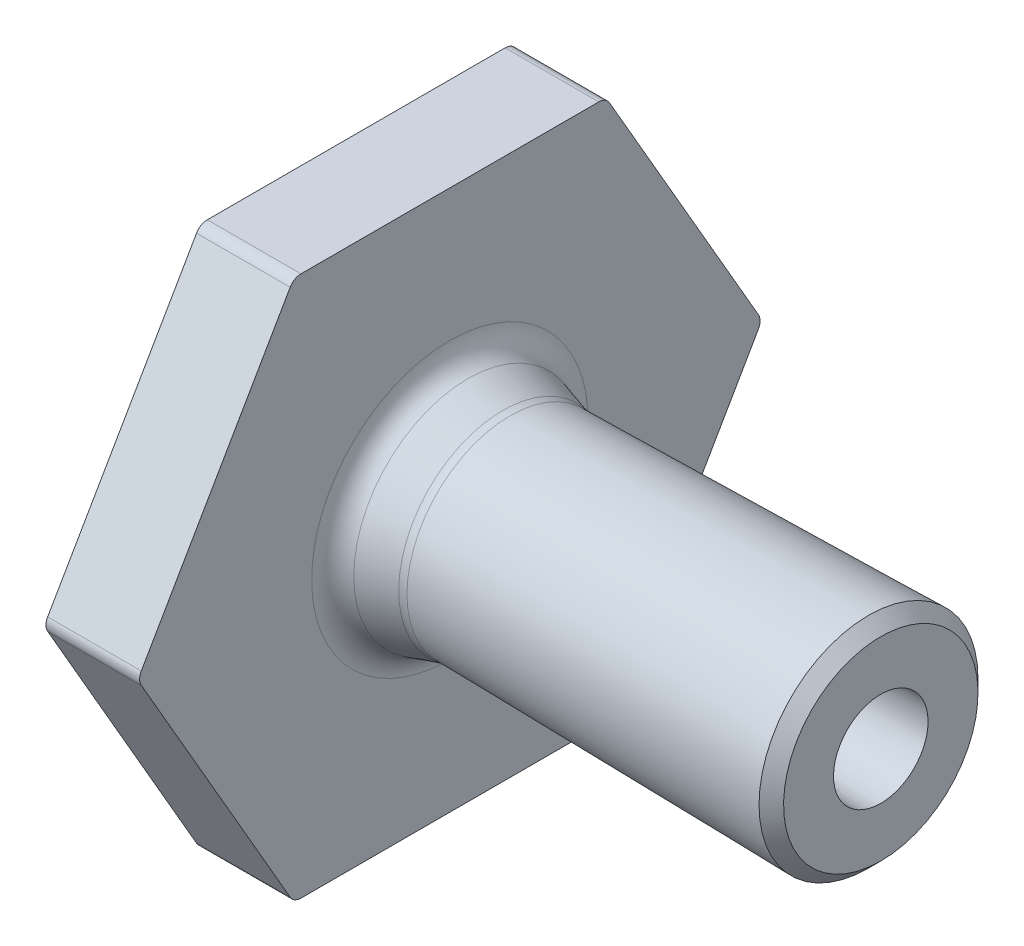
SolidWorks part; units mm, degrees
ref_plane "Front Plane" through (0, 0, 0) normal (0, 0, 1) x (1, 0, 0)
ref_plane "Top Plane" through (0, 0, 0) normal (0, 1, 0) x (1, 0, 0)
ref_plane "Right Plane" through (0, 0, 0) normal (1, 0, 0) x (0, 0, -1)
sketch "Sketch1" plane through (0, 0, 0) normal (0, 0, 1) x (1, 0, 0)
  line L0 (0, 1.825) -> (6.7189, 1.825)
  line L1 (0, -55) -> (0, 55) construction
  line L2 (6.7189, 1.825) -> (8.5498, 1.3)
  line L4 (8.5498, 1.3) -> (20.8041, 1.5139)
  line L8 (55, 0) -> (-55, 0) construction
  line L9 (0, 0) -> (20.8041, 0) construction
  line L10 (20.8041, 1.5139) -> (20.8041, 0) construction
  line L11 (0, 3.825) -> (7, 3.825) construction
  line L12 (7, 3.825) -> (8.8138, 3.3049)
  line L13 (8.8138, 3.3049) -> (20.8041, 3.5142)
  line L14 (0, 0) -> (0, 1.825) construction
  line L15 (20.8041, 1.5139) -> (4.6863, 1.5139) construction
  line L16 (0, 1.825) -> (0, 2.625)
  line L17 (7, 3.825) -> (7, 10)
  line L18 (7, 10) -> (4, 10)
  line L19 (4, 10) -> (4, 2.625)
  line L20 (0, 2.625) -> (4, 2.625)
  line L21 (0, 2.625) -> (0, 3.825) construction
  line L22 (8.8138, 3.3049) -> (20.7692, 3.5136) construction
  line L23 (20.8041, 1.5139) -> (20.8041, 3.5142)
  dimension "D1" = 1.3
  dimension "D2" = 1.5139
  dimension "D3" = 2
  dimension "D4" = 2.625
  dimension "D5" = 0.8
  dimension "D6" = 3
  dimension "D7" = 16
  dimension "D8" = 1
  dimension "D9" = 10
  dimension "D10" = 4
revolve "Revolve1" add sketch "Sketch1" angle 360 about L9
fillet "Fillet4" radius 3 2 edges at (8.5498, -1.3, 0) (6.7189, -1.825, 0)
chamfer "Chamfer1" distance 0.4 angle 45 1 edges at (20.8041, -3.5142, 0)
sketch "Sketch2" plane through (7, 0, 0) normal (1, 0, 0) x (0, 0, -1)
  line L0 (0, 0) -> (10, 0) construction
  line L1 (10, 0) -> (5, 8.6603)
  line L2 (5, 8.6603) -> (-5, 8.6603)
  line L3 (-5, 8.6603) -> (-10, 0)
  line L4 (-10, 0) -> (-5, -8.6603)
  line L5 (-5, -8.6603) -> (5, -8.6603)
  line L6 (5, -8.6603) -> (10, 0)
  circle A0 centre (0, 0) radius 8.6603 construction
  circle A1 centre (0, 0) radius 10 construction
  circle A2 centre (0, 0) radius 10
  circle M2 centre (0, 0) radius 10
extrude "Cut-Extrude1" cut sketch "Sketch2" against normal through all both and the other way through all contours L3 M2 | L2 M2 | L1 M2 | L4 M2 | L5 M2 | L6 M2
fillet "Fillet5" radius 0.4 6 edges at (5.5, 8.6603, -5) (5.5, 0, -10) (5.5, -8.6603, -5) (5.5, -8.6603, 5) (5.5, 0, 10) (5.5, 8.6603, 5)
fillet "Fillet6" radius 0.8 2 edges at (8.8138, -3.3049, 0) (7, -3.825, 0)
fillet "Fillet7" radius 0.2 1 edges at (4, -2.625, 0)
